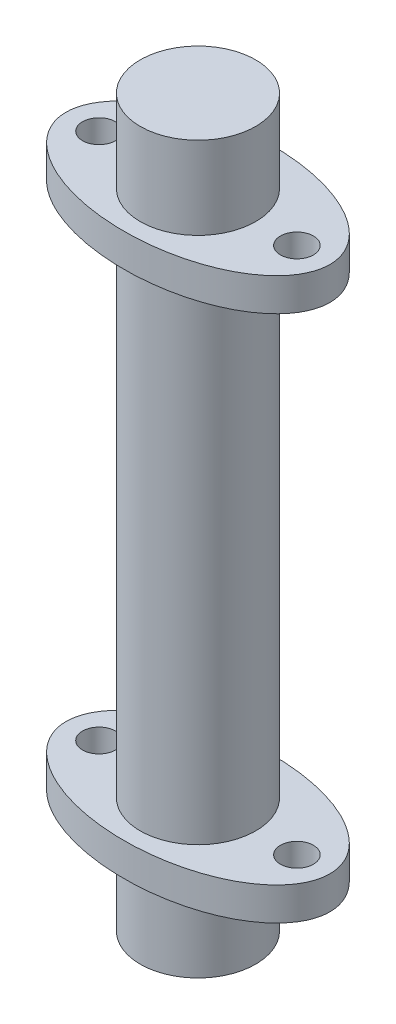
SolidWorks part; units mm, degrees
ref_plane "Plan de face" through (0, 0, 0) normal (0, 0, 1) x (1, 0, 0)
ref_plane "Plan de dessus" through (0, 0, 0) normal (0, 1, 0) x (1, 0, 0)
ref_plane "Plan de droite" through (0, 0, 0) normal (1, 0, 0) x (0, 0, -1)
sketch "Esquisse1" plane through (0, 0, 0) normal (0, 1, 0) x (1, 0, 0)
  circle A0 centre (0, 0) radius 3.5
  dimension "D1" = 7
extrude "Boss.-Extru.1" add sketch "Esquisse1" along normal blind 15
sketch "Esquisse2" plane through (0, 15, 0) normal (0, 1, 0) x (1, 0, 0)
  line L0 (0, 0) -> (10.7539, 0) construction
  line L1 (0, 0) -> (0, 8.98) construction
  circle A0 centre (6, 0) radius 1
  circle A1 centre (-6, 0) radius 1
  ellipse E0 centre (0, 0) end of major axis (8, 0) minor radius 4.5
  dimension "D3" = 2
  dimension "D1" = 8
  dimension "D2" = 9
  dimension "D4" = 6
extrude "Boss.-Extru.2" add sketch "Esquisse2" along normal blind 2
sketch "Esquisse4" plane through (0, 17, 0) normal (0, 1, 0) x (1, 0, 0)
  circle A0 centre (0, 0) radius 3.5
  dimension "D1" = 7
extrude "Boss.-Extru.3" add sketch "Esquisse4" along normal blind 5
mirror "Symétrie1" about plane through (0, 0, 0) normal (0, 1, 0) of "Boss.-Extru.1", "Boss.-Extru.2", "Boss.-Extru.3"
